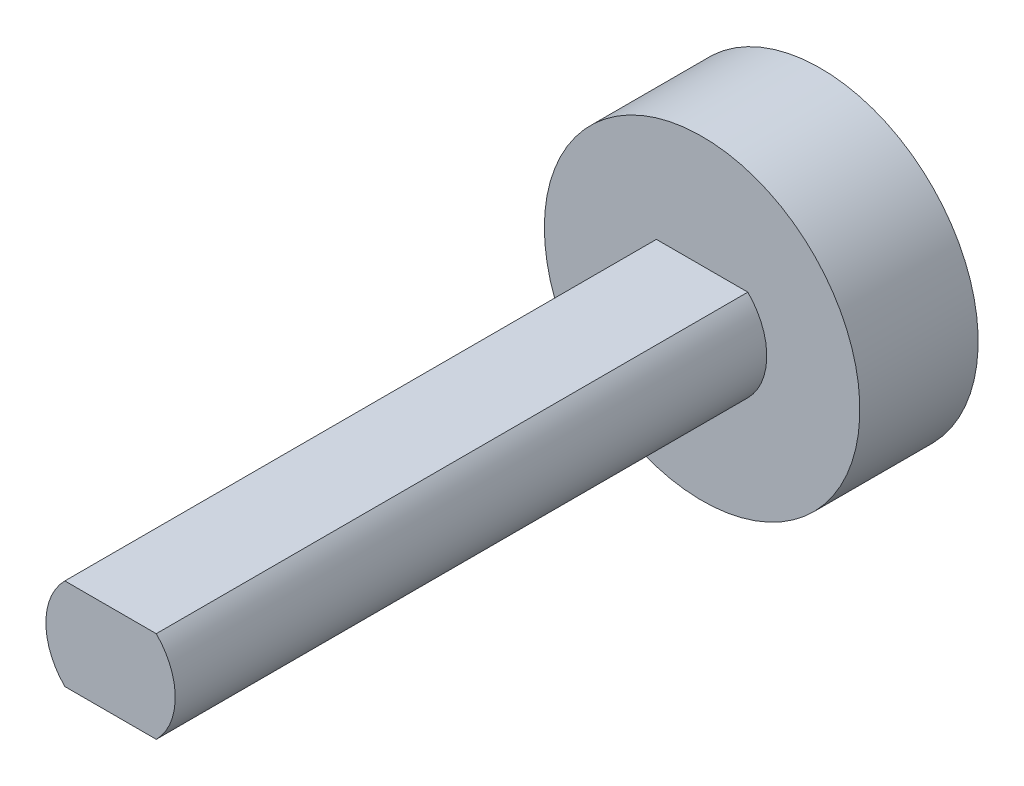
SolidWorks part; units mm, degrees
ref_plane "Front Plane" through (0, 0, 0) normal (0, 0, 1) x (1, 0, 0)
ref_plane "Top Plane" through (0, 0, 0) normal (0, 1, 0) x (1, 0, 0)
ref_plane "Right Plane" through (0, 0, 0) normal (1, 0, 0) x (0, 0, -1)
sketch "Sketch1" plane through (0, 0, 0) normal (0, 0, 1) x (1, 0, 0)
  line L1 (-7.3595, -7.3682) -> (7.3595, -7.3682)
  line L3 (-7.3595, 7.3682) -> (7.3595, 7.3682)
  arc A0 (-7.3595, 7.3682) -> (-7.3595, -7.3682) centre (0, 0) ccw
  arc A1 (7.3595, -7.3682) -> (7.3595, 7.3682) centre (0, 0) ccw
extrude "Boss-Extrude1" add sketch "Sketch1" along normal blind 114.3
sketch "Sketch3" plane through (0, 0, 0) normal (0, 0, -1) x (-1, 0, 0)
  circle A0 centre (0, 0) radius 25.402
extrude "Boss-Extrude2" add sketch "Sketch3" against normal blind 19.05
